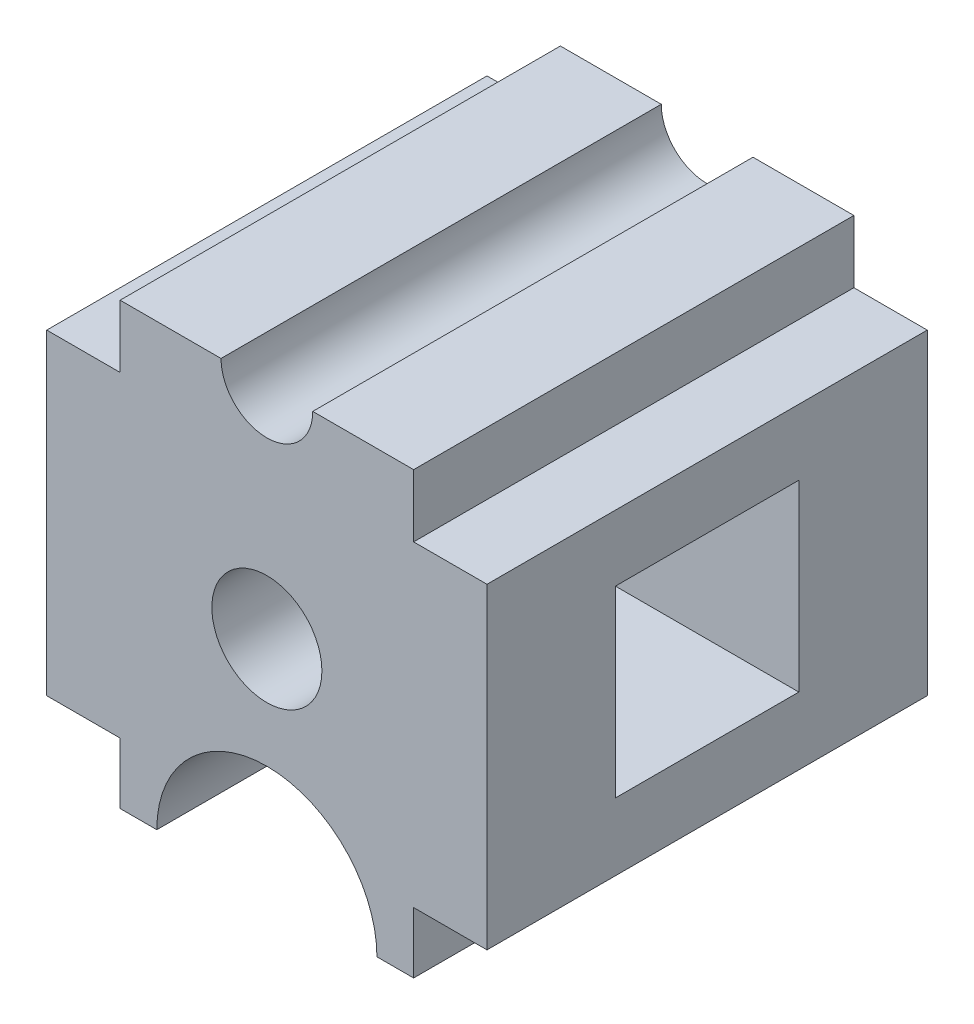
SolidWorks part; units mm, degrees
ref_plane "Front Plane" through (0, 0, 0) normal (0, 0, 1) x (1, 0, 0)
ref_plane "Top Plane" through (0, 0, 0) normal (0, 1, 0) x (1, 0, 0)
ref_plane "Right Plane" through (0, 0, 0) normal (1, 0, 0) x (0, 0, -1)
sketch "Sketch1" plane through (0, 0, 0) normal (0, 0, 1) x (1, 0, 0)
  line L0 (30, -60) -> (40, -60)
  line L1 (40, -60) -> (40, -43.3694)
  line L2 (40, -43.3694) -> (60, -43.3694)
  line L3 (60, -43.3694) -> (60, 42.9426)
  line L4 (60, 42.9426) -> (40, 42.9426)
  line L5 (40, 42.9426) -> (40, 60)
  line L6 (40, 60) -> (12.5, 60)
  line L7 (-12.5, 60) -> (-40, 60)
  line L8 (-40, 60) -> (-40, 42.9426)
  line L9 (-40, 42.9426) -> (-60, 42.9426)
  line L10 (-60, 42.9426) -> (-60, 0)
  line L11 (-60, 0) -> (-60, -43.3694)
  line L12 (-60, -43.3694) -> (-40, -43.3694)
  line L13 (-40, -43.3694) -> (-40, -60)
  line L14 (0, 200.3688) -> (0, -216.6743) construction
  line L15 (-192.3061, 0) -> (280.3565, 0) construction
  line L16 (-40, -60) -> (-30, -60)
  circle A0 centre (0, 0) radius 15
  arc A1 (30, -60) -> (-30, -60) centre (0, -60) ccw
  arc A2 (-12.5, 60) -> (12.5, 60) centre (0, 60) ccw
  dimension "D1" = 30
  dimension "D2" = 60
  dimension "D4" = 12.5
  dimension "D5" = 120
  dimension "D6" = 60
  dimension "D7" = 27.5
  dimension "D8" = 27.5
  dimension "D9" = 20
  dimension "D10" = 20
  dimension "D11" = 20
  dimension "D13" = 60
extrude "Boss-Extrude1" add sketch "Sketch1" along normal mid plane 120
sketch "Sketch2" plane through (60, 0, 0) normal (1, 0, 0) x (0, 0, -1)
  line L0 (60, -43.3694) -> (60, 42.9426) construction
  line L1 (-25, 25) -> (25, 25)
  line L2 (-25, 25) -> (-25, -25)
  line L3 (-25, -25) -> (25, -25)
  line L4 (25, 25) -> (25, -25)
  line L5 (-25, 25) -> (25, -25) construction
  line L6 (-25, -25) -> (25, 25) construction
  line L8 (-60, -60) -> (60, -60) construction
  point P0 (0, 0)
  dimension "D1" = 35
  dimension "D2" = 35
extrude "Cut-Extrude1" cut sketch "Sketch2" against normal blind 120
